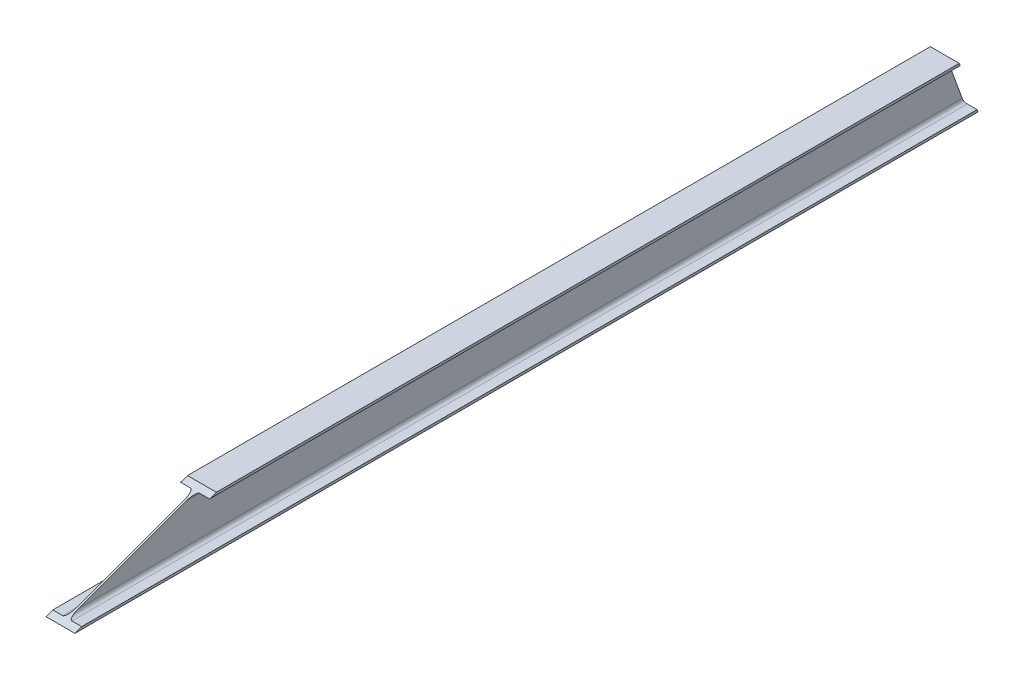
SolidWorks part; units mm, degrees
material "1.0035 (S185)"
ref_plane "Front Plane" through (0, 0, 0) normal (0, 0, 1) x (1, 0, 0)
ref_plane "Top Plane" through (0, 0, 0) normal (0, 1, 0) x (1, 0, 0)
ref_plane "Right Plane" through (0, 0, 0) normal (1, 0, 0) x (0, 0, -1)
sketch "Sketch1" plane through (0, 0, 0) normal (0, 0, 1) x (1, 0, 0)
  line L0 (-27.5, 49) -> (27.5, 49)
  line L1 (27.5, 49) -> (27.5, 44.3)
  line L2 (27.5, 44.3) -> (8.8, 44.3)
  line L3 (1.8, 37.3) -> (1.8, -37.3)
  line L4 (8.8, -44.3) -> (27.5, -44.3)
  line L5 (27.5, -44.3) -> (27.5, -49)
  line L6 (27.5, -49) -> (-27.5, -49)
  line L7 (-27.5, -49) -> (-27.5, -44.3)
  line L8 (-27.5, -44.3) -> (-8.8, -44.3)
  line L9 (-1.8, -37.3) -> (-1.8, 37.3)
  line L10 (-8.8, 44.3) -> (-27.5, 44.3)
  line L11 (-27.5, 44.3) -> (-27.5, 49)
  line L12 (-36.0742, 0) -> (31.9951, 0) construction
  arc A0 (8.8, -44.3) -> (1.8, -37.3) centre (8.8, -37.3) cw
  arc A1 (-1.8, -37.3) -> (-8.8, -44.3) centre (-8.8, -37.3) cw
  arc A2 (-8.8, 44.3) -> (-1.8, 37.3) centre (-8.8, 37.3) cw
  arc A3 (1.8, 37.3) -> (8.8, 44.3) centre (8.8, 37.3) cw
  point P23 (31.9951, 0)
  dimension "D8" = 7
  dimension "D2" = 3.6
  dimension "D3" = 4.7
  dimension "D4" = 4.7
  dimension "D5" = 1.8
  dimension "D6" = 55
  dimension "D7" = 25.7
  dimension "D1" = 98
  dimension "D9" = 49
extrude "Boss-Extrude1" add sketch "Sketch1" along normal blind 1726.3505
ref_plane "Plane1" through (0, -5.7319, 15.7483) normal (0, -0.342, 0.9397) x (1, 0, 0)
sketch "Sketch2" plane through (0, -5.7319, 15.7483) normal (0, -0.342, 0.9397) x (1, 0, 0)
  line L1 (-105.8512, -228.7626) -> (105.8512, -228.7626)
  line L2 (-105.8512, -228.7626) -> (-105.8512, 254.8243)
  line L3 (-105.8512, 254.8243) -> (105.8512, 254.8243)
  line L4 (105.8512, -228.7626) -> (105.8512, 254.8243)
  line L5 (-105.8512, -228.7626) -> (105.8512, 254.8243) construction
  line L6 (-105.8512, 254.8243) -> (105.8512, -228.7626) construction
  point P0 (0, 13.0309)
extrude "Cut-Extrude1" cut sketch "Sketch2" against normal through all
ref_plane "Plane2" through (0, 0, 1726.3505) normal (0, 0, 1) x (1, 0, 0)
ref_plane "Plane3" through (0, 511.5703, 186.1964) normal (0, 0.9397, 0.342) x (1, 0, 0)
sketch "Sketch3" plane through (0, 511.5703, 186.1964) normal (0, 0.9397, 0.342) x (1, 0, 0)
  line L1 (-65.5847, -1763.4513) -> (135.0271, -1763.4513)
  line L2 (-65.5847, -1763.4513) -> (-65.5847, -906.0296)
  line L3 (-65.5847, -906.0296) -> (135.0271, -906.0296)
  line L4 (135.0271, -1763.4513) -> (135.0271, -906.0296)
  line L5 (-65.5847, -1763.4513) -> (135.0271, -906.0296) construction
  line L6 (-65.5847, -906.0296) -> (135.0271, -1763.4513) construction
  point P0 (34.7212, -1334.7405)
extrude "Cut-Extrude3" cut sketch "Sketch3" against normal blind 2.54 and the other way through all
sketch "Sketch5" plane through (0, -5.7319, 15.7483) normal (0, 0.342, -0.9397) x (-1, 0, 0)
  line L1 (1.8, -33.5941) -> (1.8, 45.7936) construction
  point P0 (0, 6.0998)
  point P1 (0, 0)
  point P4 (0, 0)
  point P7 (1.8, 6.0998)
equation "\"D4@Sketch1\"=\"D3@Sketch1\""
equation "\"D5@Sketch1\"=\"D2@Sketch1\"/2"
equation "\"D7@Sketch1\"=(\"D6@Sketch1\"-\"D2@Sketch1\")/2"
equation "\"D9@Sketch1\"=\"D1@Sketch1\"/2"
